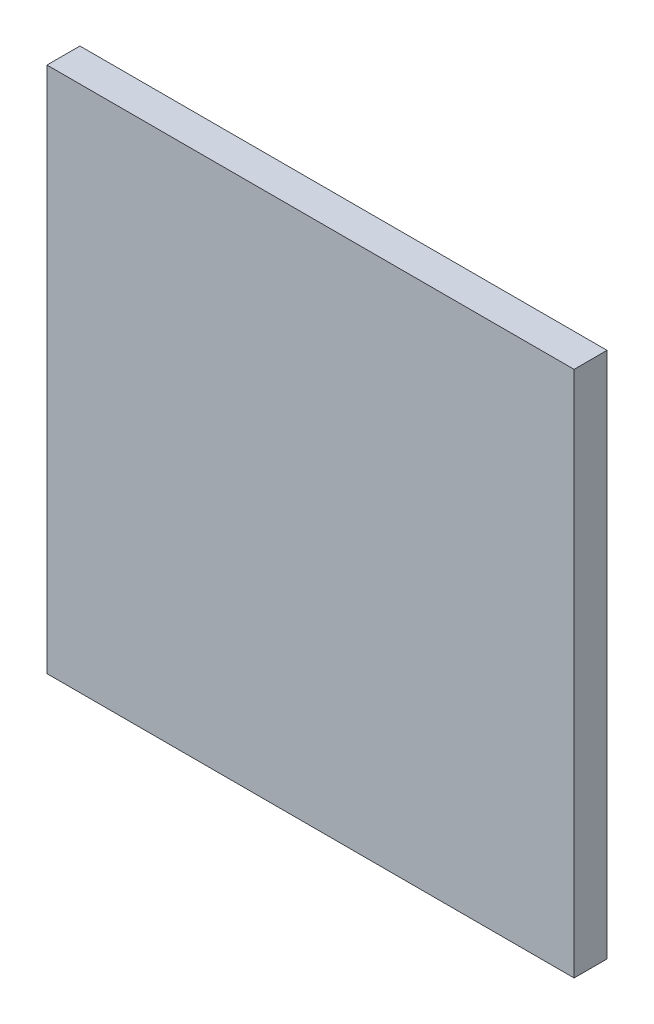
SolidWorks part; units mm, degrees
ref_plane "Front Plane" through (0, 0, 0) normal (0, 0, 1) x (1, 0, 0)
ref_plane "Top Plane" through (0, 0, 0) normal (0, 1, 0) x (1, 0, 0)
ref_plane "Right Plane" through (0, 0, 0) normal (1, 0, 0) x (0, 0, -1)
sketch "Sketch1" plane through (0, 0, 0) normal (0, 0, 1) x (1, 0, 0)
  line L1 (0, 0) -> (40, 0)
  line L2 (0, 0) -> (0, 40)
  line L3 (0, 40) -> (40, 40)
  line L4 (40, 0) -> (40, 40)
  dimension "D1" = 40
  dimension "D2" = 40
extrude "Boss-Extrude1" add sketch "Sketch1" along normal blind 2.5
